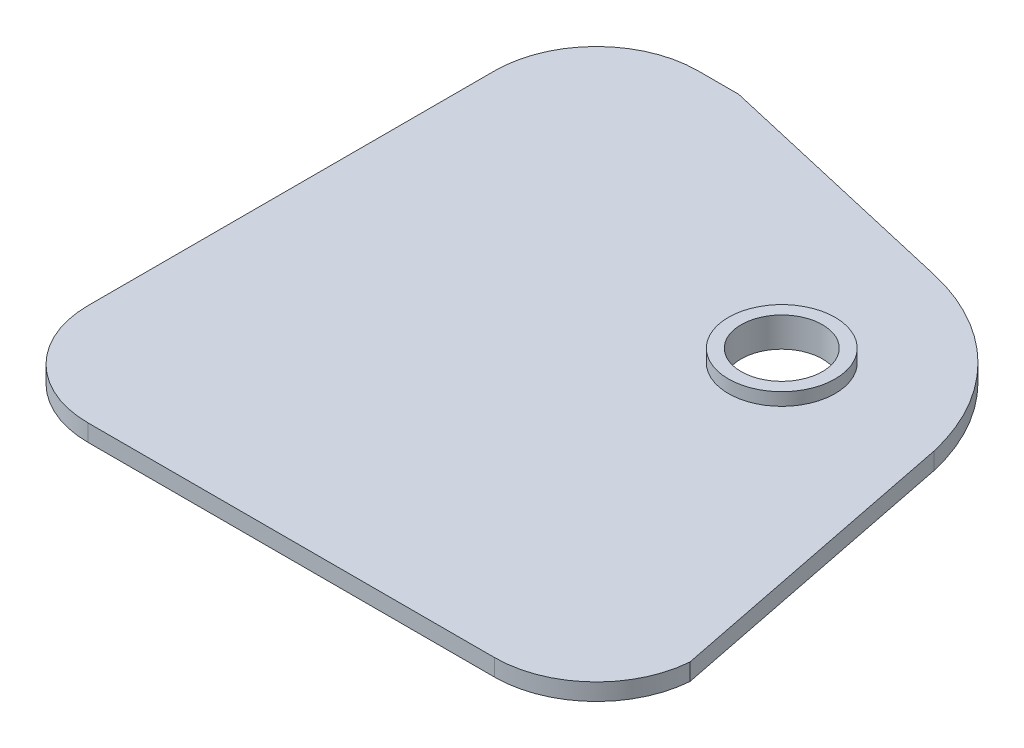
SolidWorks part; units mm, degrees
ref_plane "Front" through (0, 0, 0) normal (0, 0, 1) x (1, 0, 0)
ref_plane "Top" through (0, 0, 0) normal (0, 1, 0) x (1, 0, 0)
ref_plane "Right" through (0, 0, 0) normal (1, 0, 0) x (0, 0, -1)
sketch "Sketch1" plane through (0, 0, 0) normal (0, 1, 0) x (1, 0, 0)
  line L0 (-25.4, 50.8) -> (-20.32, 50.8)
  line L3 (25.4, -25.4) -> (-25.4, -25.4)
  line L4 (-38.1, 38.1) -> (-38.1, -12.7)
  line L8 (0, -55) -> (0, 55) construction
  line L9 (-55, 0) -> (55, 0) construction
  line L11 (11.43, 24.4361) -> (54.5191, 24.4361) construction
  line L12 (-20.32, 50.8) -> (11.43, 43.4861)
  line L13 (38.0634, -13.6639) -> (30.48, 24.4361)
  circle A1 centre (11.43, 24.4361) radius 5.08
  arc A2 (-38.1, 38.1) -> (-25.4, 50.8) centre (-25.4, 38.1) cw
  arc A3 (11.43, 43.4861) -> (30.48, 24.4361) centre (5.7282, 18.7344) cw
  arc A4 (25.4, -25.4) -> (38.0634, -13.6639) centre (25.4, -12.7) ccw
  arc A5 (-38.1, -12.7) -> (-25.4, -25.4) centre (-25.4, -12.7) ccw
  point P0 (0, 0)
  point P6 (30.48, 24.436)
  point P10 (31.3554, 24.4361)
  point P13 (-38.1, 50.8)
  point P17 (0, 0)
  point P20 (38.1, -25.4)
  point P23 (-38.1, -25.4)
  point P24 (0, 0)
  point P28 (0, 0)
  point P29 (0, 0)
  dimension "D3" = 25.4
  dimension "D6" = 10.16
  dimension "D5" = 12.7
  dimension "D7" = 38.1
  dimension "D8" = 12.7
  dimension "D9" = 12.7
  dimension "D14" = 6.35
  dimension "D15" = 38.1
  dimension "D1" = 76.2
  dimension "D2" = 76.2
  dimension "D4" = 31.75
  dimension "D10" = 19.05
  dimension "D11" = 38.1
  dimension "D12" = 19.05
  dimension "D13" = 25.4
extrude "Boss-Extrude1" add sketch "Sketch1" along normal blind 2.1167
sketch "Sketch2" plane through (0, 2.1167, 0) normal (0, 1, 0) x (1, 0, 0)
  circle A0 centre (11.43, 24.4361) radius 5.08 construction
  circle A1 centre (11.43, 24.4361) radius 5.08
  circle A2 centre (11.43, 24.4361) radius 6.6675
  dimension "D1" = 1.5875
extrude "Boss-Extrude2" add sketch "Sketch2" along normal blind 1.5875
